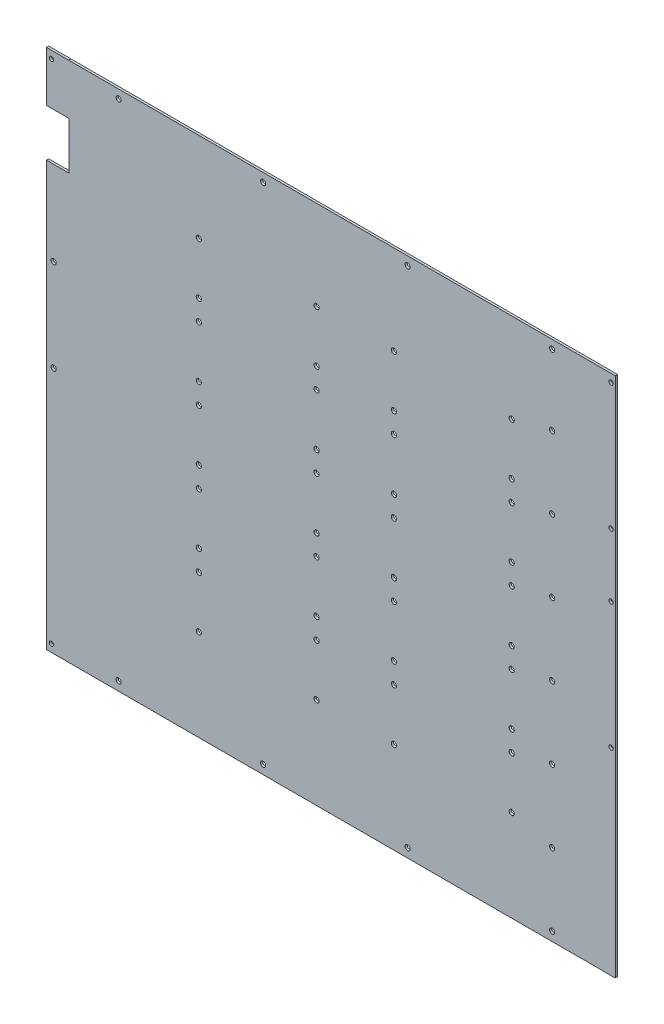
SolidWorks part; units mm, degrees
ref_plane "Front Plane" through (0, 0, 0) normal (0, 0, 1) x (1, 0, 0)
ref_plane "Top Plane" through (0, 0, 0) normal (0, 1, 0) x (1, 0, 0)
ref_plane "Right Plane" through (0, 0, 0) normal (1, 0, 0) x (0, 0, -1)
sketch "Model" plane through (0, 0, 0) normal (0, 0, 1) x (1, 0, 0)
  line L0 (0, 0) -> (400.05, 0)
  line L1 (400.05, 0) -> (400.05, 366.722)
  line L2 (400.05, 366.722) -> (15.6398, 366.7222)
  line L3 (15.6398, 366.7222) -> (0, 366.7222)
  line L4 (0, 366.7222) -> (0, 331.3716)
  line L5 (0, 331.3716) -> (15.748, 331.3716)
  line L6 (15.748, 331.3716) -> (15.748, 298.0477)
  line L7 (15.748, 298.0477) -> (0, 298.0477)
  line L8 (0, 298.0477) -> (0, 0)
  line L2009 (3.556, 361.188) -> (3.556, 361.696)
  line L2010 (3.302, 361.442) -> (3.81, 361.442)
  line L2011 (3.556, 361.188) -> (3.556, 361.696)
  line L2012 (3.302, 361.442) -> (3.81, 361.442)
  line L2013 (3.556, 361.188) -> (3.556, 361.696)
  line L2014 (3.302, 361.442) -> (3.81, 361.442)
  line L2015 (3.556, 361.188) -> (3.556, 361.696)
  line L2016 (3.302, 361.442) -> (3.81, 361.442)
  line L2017 (3.556, 361.188) -> (3.556, 361.696)
  line L2018 (3.302, 361.442) -> (3.81, 361.442)
  line L2019 (3.556, 361.188) -> (3.556, 361.696)
  line L2020 (3.302, 361.442) -> (3.81, 361.442)
  line L2021 (3.556, 361.188) -> (3.556, 361.696)
  line L2022 (3.302, 361.442) -> (3.81, 361.442)
  line L2023 (3.556, 361.188) -> (3.556, 361.696)
  line L2024 (3.302, 361.442) -> (3.81, 361.442)
  line L2025 (3.556, 5.08) -> (3.556, 5.588)
  line L2026 (3.302, 5.334) -> (3.81, 5.334)
  line L2027 (3.556, 5.08) -> (3.556, 5.588)
  line L2028 (3.302, 5.334) -> (3.81, 5.334)
  line L2029 (3.556, 5.08) -> (3.556, 5.588)
  line L2030 (3.302, 5.334) -> (3.81, 5.334)
  line L2031 (3.556, 5.08) -> (3.556, 5.588)
  line L2032 (3.302, 5.334) -> (3.81, 5.334)
  line L2033 (3.556, 5.08) -> (3.556, 5.588)
  line L2034 (3.302, 5.334) -> (3.81, 5.334)
  line L2035 (3.556, 5.08) -> (3.556, 5.588)
  line L2036 (3.302, 5.334) -> (3.81, 5.334)
  line L2037 (3.556, 5.08) -> (3.556, 5.588)
  line L2038 (3.302, 5.334) -> (3.81, 5.334)
  line L2039 (3.556, 5.08) -> (3.556, 5.588)
  line L2040 (3.302, 5.334) -> (3.81, 5.334)
  line L2041 (5.08, 238.506) -> (5.08, 239.014)
  line L2042 (4.826, 238.76) -> (5.334, 238.76)
  line L2043 (5.08, 238.506) -> (5.08, 239.014)
  line L2044 (4.826, 238.76) -> (5.334, 238.76)
  line L2045 (5.08, 238.506) -> (5.08, 239.014)
  line L2046 (4.826, 238.76) -> (5.334, 238.76)
  line L2047 (5.08, 238.506) -> (5.08, 239.014)
  line L2048 (4.826, 238.76) -> (5.334, 238.76)
  line L2049 (5.08, 238.506) -> (5.08, 239.014)
  line L2050 (4.826, 238.76) -> (5.334, 238.76)
  line L2051 (5.08, 238.506) -> (5.08, 239.014)
  line L2052 (4.826, 238.76) -> (5.334, 238.76)
  line L2053 (5.08, 238.506) -> (5.08, 239.014)
  line L2054 (4.826, 238.76) -> (5.334, 238.76)
  line L2055 (5.08, 238.506) -> (5.08, 239.014)
  line L2056 (4.826, 238.76) -> (5.334, 238.76)
  line L2057 (5.08, 173.736) -> (5.08, 174.244)
  line L2058 (4.826, 173.99) -> (5.334, 173.99)
  line L2059 (5.08, 173.736) -> (5.08, 174.244)
  line L2060 (4.826, 173.99) -> (5.334, 173.99)
  line L2061 (5.08, 173.736) -> (5.08, 174.244)
  line L2062 (4.826, 173.99) -> (5.334, 173.99)
  line L2063 (5.08, 173.736) -> (5.08, 174.244)
  line L2064 (4.826, 173.99) -> (5.334, 173.99)
  line L2065 (5.08, 173.736) -> (5.08, 174.244)
  line L2066 (4.826, 173.99) -> (5.334, 173.99)
  line L2067 (5.08, 173.736) -> (5.08, 174.244)
  line L2068 (4.826, 173.99) -> (5.334, 173.99)
  line L2069 (5.08, 173.736) -> (5.08, 174.244)
  line L2070 (4.826, 173.99) -> (5.334, 173.99)
  line L2071 (5.08, 173.736) -> (5.08, 174.244)
  line L2072 (4.826, 173.99) -> (5.334, 173.99)
  line L3769 (397.3068, 272.2372) -> (396.7988, 272.2372)
  line L3770 (397.0528, 271.9832) -> (397.0528, 272.4912)
  line L3771 (397.3068, 272.2372) -> (396.7988, 272.2372)
  line L3772 (397.0528, 271.9832) -> (397.0528, 272.4912)
  line L3773 (397.3068, 272.2372) -> (396.7988, 272.2372)
  line L3774 (397.0528, 271.9832) -> (397.0528, 272.4912)
  line L3775 (397.3068, 272.2372) -> (396.7988, 272.2372)
  line L3776 (397.0528, 271.9832) -> (397.0528, 272.4912)
  line L3777 (397.3068, 272.2372) -> (396.7988, 272.2372)
  line L3778 (397.0528, 271.9832) -> (397.0528, 272.4912)
  line L3779 (397.3068, 272.2372) -> (396.7988, 272.2372)
  line L3780 (397.0528, 271.9832) -> (397.0528, 272.4912)
  line L3781 (397.3068, 272.2372) -> (396.7988, 272.2372)
  line L3782 (397.0528, 271.9832) -> (397.0528, 272.4912)
  line L3783 (397.3068, 272.2372) -> (396.7988, 272.2372)
  line L3784 (397.0528, 271.9832) -> (397.0528, 272.4912)
  line L3785 (397.3068, 361.1372) -> (396.7988, 361.1372)
  line L3786 (397.0528, 360.8832) -> (397.0528, 361.3912)
  line L3787 (397.3068, 361.1372) -> (396.7988, 361.1372)
  line L3788 (397.0528, 360.8832) -> (397.0528, 361.3912)
  line L3789 (397.3068, 361.1372) -> (396.7988, 361.1372)
  line L3790 (397.0528, 360.8832) -> (397.0528, 361.3912)
  line L3791 (397.3068, 361.1372) -> (396.7988, 361.1372)
  line L3792 (397.0528, 360.8832) -> (397.0528, 361.3912)
  line L3793 (397.3068, 361.1372) -> (396.7988, 361.1372)
  line L3794 (397.0528, 360.8832) -> (397.0528, 361.3912)
  line L3795 (397.3068, 361.1372) -> (396.7988, 361.1372)
  line L3796 (397.0528, 360.8832) -> (397.0528, 361.3912)
  line L3797 (397.3068, 361.1372) -> (396.7988, 361.1372)
  line L3798 (397.0528, 360.8832) -> (397.0528, 361.3912)
  line L3799 (397.3068, 361.1372) -> (396.7988, 361.1372)
  line L3800 (397.0528, 360.8832) -> (397.0528, 361.3912)
  line L5337 (397.3068, 138.8872) -> (396.7988, 138.8872)
  line L5338 (397.0528, 138.6332) -> (397.0528, 139.1412)
  line L5339 (397.3068, 138.8872) -> (396.7988, 138.8872)
  line L5340 (397.0528, 138.6332) -> (397.0528, 139.1412)
  line L5341 (397.3068, 138.8872) -> (396.7988, 138.8872)
  line L5342 (397.0528, 138.6332) -> (397.0528, 139.1412)
  line L5343 (397.3068, 138.8872) -> (396.7988, 138.8872)
  line L5344 (397.0528, 138.6332) -> (397.0528, 139.1412)
  line L5345 (397.3068, 138.8872) -> (396.7988, 138.8872)
  line L5346 (397.0528, 138.6332) -> (397.0528, 139.1412)
  line L5347 (397.3068, 138.8872) -> (396.7988, 138.8872)
  line L5348 (397.0528, 138.6332) -> (397.0528, 139.1412)
  line L5349 (397.3068, 138.8872) -> (396.7988, 138.8872)
  line L5350 (397.0528, 138.6332) -> (397.0528, 139.1412)
  line L5351 (397.3068, 138.8872) -> (396.7988, 138.8872)
  line L5352 (397.0528, 138.6332) -> (397.0528, 139.1412)
  line L5353 (397.3068, 227.7872) -> (396.7988, 227.7872)
  line L5354 (397.0528, 227.5332) -> (397.0528, 228.0412)
  line L5355 (397.3068, 227.7872) -> (396.7988, 227.7872)
  line L5356 (397.0528, 227.5332) -> (397.0528, 228.0412)
  line L5357 (397.3068, 227.7872) -> (396.7988, 227.7872)
  line L5358 (397.0528, 227.5332) -> (397.0528, 228.0412)
  line L5359 (397.3068, 227.7872) -> (396.7988, 227.7872)
  line L5360 (397.0528, 227.5332) -> (397.0528, 228.0412)
  line L5361 (397.3068, 227.7872) -> (396.7988, 227.7872)
  line L5362 (397.0528, 227.5332) -> (397.0528, 228.0412)
  line L5363 (397.3068, 227.7872) -> (396.7988, 227.7872)
  line L5364 (397.0528, 227.5332) -> (397.0528, 228.0412)
  line L5365 (397.3068, 227.7872) -> (396.7988, 227.7872)
  line L5366 (397.0528, 227.5332) -> (397.0528, 228.0412)
  line L5367 (397.3068, 227.7872) -> (396.7988, 227.7872)
  line L5368 (397.0528, 227.5332) -> (397.0528, 228.0412)
  line L7017 (355.6, 360.426) -> (355.6, 360.934)
  line L7018 (355.346, 360.68) -> (355.854, 360.68)
  line L7019 (355.6, 360.426) -> (355.6, 360.934)
  line L7020 (355.346, 360.68) -> (355.854, 360.68)
  line L7021 (355.6, 360.426) -> (355.6, 360.934)
  line L7022 (355.346, 360.68) -> (355.854, 360.68)
  line L7023 (355.6, 360.426) -> (355.6, 360.934)
  line L7024 (355.346, 360.68) -> (355.854, 360.68)
  line L7025 (355.6, 360.426) -> (355.6, 360.934)
  line L7026 (355.346, 360.68) -> (355.854, 360.68)
  line L7027 (355.6, 360.426) -> (355.6, 360.934)
  line L7028 (355.346, 360.68) -> (355.854, 360.68)
  line L7029 (355.6, 360.426) -> (355.6, 360.934)
  line L7030 (355.346, 360.68) -> (355.854, 360.68)
  line L7031 (355.6, 360.426) -> (355.6, 360.934)
  line L7032 (355.346, 360.68) -> (355.854, 360.68)
  line L7033 (355.6, 310.896) -> (355.6, 311.404)
  line L7034 (355.346, 311.15) -> (355.854, 311.15)
  line L7035 (355.6, 310.896) -> (355.6, 311.404)
  line L7036 (355.346, 311.15) -> (355.854, 311.15)
  line L7037 (355.6, 310.896) -> (355.6, 311.404)
  line L7038 (355.346, 311.15) -> (355.854, 311.15)
  line L7039 (355.6, 310.896) -> (355.6, 311.404)
  line L7040 (355.346, 311.15) -> (355.854, 311.15)
  line L7041 (355.6, 310.896) -> (355.6, 311.404)
  line L7042 (355.346, 311.15) -> (355.854, 311.15)
  line L7043 (355.6, 310.896) -> (355.6, 311.404)
  line L7044 (355.346, 311.15) -> (355.854, 311.15)
  line L7045 (355.6, 310.896) -> (355.6, 311.404)
  line L7046 (355.346, 311.15) -> (355.854, 311.15)
  line L7047 (355.6, 310.896) -> (355.6, 311.404)
  line L7048 (355.346, 311.15) -> (355.854, 311.15)
  line L7049 (355.6, 260.096) -> (355.6, 260.604)
  line L7050 (355.346, 260.35) -> (355.854, 260.35)
  line L7051 (355.6, 260.096) -> (355.6, 260.604)
  line L7052 (355.346, 260.35) -> (355.854, 260.35)
  line L7053 (355.6, 260.096) -> (355.6, 260.604)
  line L7054 (355.346, 260.35) -> (355.854, 260.35)
  line L7055 (355.6, 260.096) -> (355.6, 260.604)
  line L7056 (355.346, 260.35) -> (355.854, 260.35)
  line L7057 (355.6, 260.096) -> (355.6, 260.604)
  line L7058 (355.346, 260.35) -> (355.854, 260.35)
  line L7059 (355.6, 260.096) -> (355.6, 260.604)
  line L7060 (355.346, 260.35) -> (355.854, 260.35)
  line L7061 (355.6, 260.096) -> (355.6, 260.604)
  line L7062 (355.346, 260.35) -> (355.854, 260.35)
  line L7063 (355.6, 260.096) -> (355.6, 260.604)
  line L7064 (355.346, 260.35) -> (355.854, 260.35)
  line L7065 (355.6, 209.296) -> (355.6, 209.804)
  line L7066 (355.346, 209.55) -> (355.854, 209.55)
  line L7067 (355.6, 209.296) -> (355.6, 209.804)
  line L7068 (355.346, 209.55) -> (355.854, 209.55)
  line L7069 (355.6, 209.296) -> (355.6, 209.804)
  line L7070 (355.346, 209.55) -> (355.854, 209.55)
  line L7071 (355.6, 209.296) -> (355.6, 209.804)
  line L7072 (355.346, 209.55) -> (355.854, 209.55)
  line L7073 (355.6, 209.296) -> (355.6, 209.804)
  line L7074 (355.346, 209.55) -> (355.854, 209.55)
  line L7075 (355.6, 209.296) -> (355.6, 209.804)
  line L7076 (355.346, 209.55) -> (355.854, 209.55)
  line L7077 (355.6, 209.296) -> (355.6, 209.804)
  line L7078 (355.346, 209.55) -> (355.854, 209.55)
  line L7079 (355.6, 209.296) -> (355.6, 209.804)
  line L7080 (355.346, 209.55) -> (355.854, 209.55)
  line L7081 (355.6, 158.496) -> (355.6, 159.004)
  line L7082 (355.346, 158.75) -> (355.854, 158.75)
  line L7083 (355.6, 158.496) -> (355.6, 159.004)
  line L7084 (355.346, 158.75) -> (355.854, 158.75)
  line L7085 (355.6, 158.496) -> (355.6, 159.004)
  line L7086 (355.346, 158.75) -> (355.854, 158.75)
  line L7087 (355.6, 158.496) -> (355.6, 159.004)
  line L7088 (355.346, 158.75) -> (355.854, 158.75)
  line L7089 (355.6, 158.496) -> (355.6, 159.004)
  line L7090 (355.346, 158.75) -> (355.854, 158.75)
  line L7091 (355.6, 158.496) -> (355.6, 159.004)
  line L7092 (355.346, 158.75) -> (355.854, 158.75)
  line L7093 (355.6, 158.496) -> (355.6, 159.004)
  line L7094 (355.346, 158.75) -> (355.854, 158.75)
  line L7095 (355.6, 158.496) -> (355.6, 159.004)
  line L7096 (355.346, 158.75) -> (355.854, 158.75)
  line L7097 (355.6, 107.696) -> (355.6, 108.204)
  line L7098 (355.346, 107.95) -> (355.854, 107.95)
  line L7099 (355.6, 107.696) -> (355.6, 108.204)
  line L7100 (355.346, 107.95) -> (355.854, 107.95)
  line L7101 (355.6, 107.696) -> (355.6, 108.204)
  line L7102 (355.346, 107.95) -> (355.854, 107.95)
  line L7103 (355.6, 107.696) -> (355.6, 108.204)
  line L7104 (355.346, 107.95) -> (355.854, 107.95)
  line L7105 (355.6, 107.696) -> (355.6, 108.204)
  line L7106 (355.346, 107.95) -> (355.854, 107.95)
  line L7107 (355.6, 107.696) -> (355.6, 108.204)
  line L7108 (355.346, 107.95) -> (355.854, 107.95)
  line L7109 (355.6, 107.696) -> (355.6, 108.204)
  line L7110 (355.346, 107.95) -> (355.854, 107.95)
  line L7111 (355.6, 107.696) -> (355.6, 108.204)
  line L7112 (355.346, 107.95) -> (355.854, 107.95)
  line L7113 (355.6, 56.896) -> (355.6, 57.404)
  line L7114 (355.346, 57.15) -> (355.854, 57.15)
  line L7115 (355.6, 56.896) -> (355.6, 57.404)
  line L7116 (355.346, 57.15) -> (355.854, 57.15)
  line L7117 (355.6, 56.896) -> (355.6, 57.404)
  line L7118 (355.346, 57.15) -> (355.854, 57.15)
  line L7119 (355.6, 56.896) -> (355.6, 57.404)
  line L7120 (355.346, 57.15) -> (355.854, 57.15)
  line L7121 (355.6, 56.896) -> (355.6, 57.404)
  line L7122 (355.346, 57.15) -> (355.854, 57.15)
  line L7123 (355.6, 56.896) -> (355.6, 57.404)
  line L7124 (355.346, 57.15) -> (355.854, 57.15)
  line L7125 (355.6, 56.896) -> (355.6, 57.404)
  line L7126 (355.346, 57.15) -> (355.854, 57.15)
  line L7127 (355.6, 56.896) -> (355.6, 57.404)
  line L7128 (355.346, 57.15) -> (355.854, 57.15)
  line L7129 (355.6, 6.096) -> (355.6, 6.604)
  line L7130 (355.346, 6.35) -> (355.854, 6.35)
  line L7131 (355.6, 6.096) -> (355.6, 6.604)
  line L7132 (355.346, 6.35) -> (355.854, 6.35)
  line L7133 (355.6, 6.096) -> (355.6, 6.604)
  line L7134 (355.346, 6.35) -> (355.854, 6.35)
  line L7135 (355.6, 6.096) -> (355.6, 6.604)
  line L7136 (355.346, 6.35) -> (355.854, 6.35)
  line L7137 (355.6, 6.096) -> (355.6, 6.604)
  line L7138 (355.346, 6.35) -> (355.854, 6.35)
  line L7139 (355.6, 6.096) -> (355.6, 6.604)
  line L7140 (355.346, 6.35) -> (355.854, 6.35)
  line L7141 (355.6, 6.096) -> (355.6, 6.604)
  line L7142 (355.346, 6.35) -> (355.854, 6.35)
  line L7143 (355.6, 6.096) -> (355.6, 6.604)
  line L7144 (355.346, 6.35) -> (355.854, 6.35)
  line L7145 (254, 360.426) -> (254, 360.934)
  line L7146 (253.746, 360.68) -> (254.254, 360.68)
  line L7147 (254, 360.426) -> (254, 360.934)
  line L7148 (253.746, 360.68) -> (254.254, 360.68)
  line L7149 (254, 360.426) -> (254, 360.934)
  line L7150 (253.746, 360.68) -> (254.254, 360.68)
  line L7151 (254, 360.426) -> (254, 360.934)
  line L7152 (253.746, 360.68) -> (254.254, 360.68)
  line L7153 (254, 360.426) -> (254, 360.934)
  line L7154 (253.746, 360.68) -> (254.254, 360.68)
  line L7155 (254, 360.426) -> (254, 360.934)
  line L7156 (253.746, 360.68) -> (254.254, 360.68)
  line L7157 (254, 360.426) -> (254, 360.934)
  line L7158 (253.746, 360.68) -> (254.254, 360.68)
  line L7159 (254, 360.426) -> (254, 360.934)
  line L7160 (253.746, 360.68) -> (254.254, 360.68)
  line L7161 (254, 6.096) -> (254, 6.604)
  line L7162 (253.746, 6.35) -> (254.254, 6.35)
  line L7163 (254, 6.096) -> (254, 6.604)
  line L7164 (253.746, 6.35) -> (254.254, 6.35)
  line L7165 (254, 6.096) -> (254, 6.604)
  line L7166 (253.746, 6.35) -> (254.254, 6.35)
  line L7167 (254, 6.096) -> (254, 6.604)
  line L7168 (253.746, 6.35) -> (254.254, 6.35)
  line L7169 (254, 6.096) -> (254, 6.604)
  line L7170 (253.746, 6.35) -> (254.254, 6.35)
  line L7171 (254, 6.096) -> (254, 6.604)
  line L7172 (253.746, 6.35) -> (254.254, 6.35)
  line L7173 (254, 6.096) -> (254, 6.604)
  line L7174 (253.746, 6.35) -> (254.254, 6.35)
  line L7175 (254, 6.096) -> (254, 6.604)
  line L7176 (253.746, 6.35) -> (254.254, 6.35)
  line L7273 (327.152, 267.843) -> (327.152, 267.335)
  line L7274 (327.406, 267.589) -> (326.898, 267.589)
  line L7275 (327.152, 267.843) -> (327.152, 267.335)
  line L7276 (327.406, 267.589) -> (326.898, 267.589)
  line L7277 (327.152, 267.843) -> (327.152, 267.335)
  line L7278 (327.406, 267.589) -> (326.898, 267.589)
  line L7279 (327.152, 267.843) -> (327.152, 267.335)
  line L7280 (327.406, 267.589) -> (326.898, 267.589)
  line L7281 (327.152, 267.843) -> (327.152, 267.335)
  line L7282 (327.406, 267.589) -> (326.898, 267.589)
  line L7283 (327.152, 267.843) -> (327.152, 267.335)
  line L7284 (327.406, 267.589) -> (326.898, 267.589)
  line L7285 (327.152, 267.843) -> (327.152, 267.335)
  line L7286 (327.406, 267.589) -> (326.898, 267.589)
  line L7287 (327.152, 267.843) -> (327.152, 267.335)
  line L7288 (327.406, 267.589) -> (326.898, 267.589)
  line L7289 (244.348, 267.843) -> (244.348, 267.335)
  line L7290 (244.602, 267.589) -> (244.094, 267.589)
  line L7291 (244.348, 267.843) -> (244.348, 267.335)
  line L7292 (244.602, 267.589) -> (244.094, 267.589)
  line L7293 (244.348, 267.843) -> (244.348, 267.335)
  line L7294 (244.602, 267.589) -> (244.094, 267.589)
  line L7295 (244.348, 267.843) -> (244.348, 267.335)
  line L7296 (244.602, 267.589) -> (244.094, 267.589)
  line L7297 (244.348, 267.843) -> (244.348, 267.335)
  line L7298 (244.602, 267.589) -> (244.094, 267.589)
  line L7299 (244.348, 267.843) -> (244.348, 267.335)
  line L7300 (244.602, 267.589) -> (244.094, 267.589)
  line L7301 (244.348, 267.843) -> (244.348, 267.335)
  line L7302 (244.602, 267.589) -> (244.094, 267.589)
  line L7303 (244.348, 267.843) -> (244.348, 267.335)
  line L7304 (244.602, 267.589) -> (244.094, 267.589)
  line L7305 (327.152, 304.165) -> (327.152, 303.657)
  line L7306 (327.406, 303.911) -> (326.898, 303.911)
  line L7307 (327.152, 304.165) -> (327.152, 303.657)
  line L7308 (327.406, 303.911) -> (326.898, 303.911)
  line L7309 (327.152, 304.165) -> (327.152, 303.657)
  line L7310 (327.406, 303.911) -> (326.898, 303.911)
  line L7311 (327.152, 304.165) -> (327.152, 303.657)
  line L7312 (327.406, 303.911) -> (326.898, 303.911)
  line L7313 (327.152, 304.165) -> (327.152, 303.657)
  line L7314 (327.406, 303.911) -> (326.898, 303.911)
  line L7315 (327.152, 304.165) -> (327.152, 303.657)
  line L7316 (327.406, 303.911) -> (326.898, 303.911)
  line L7317 (327.152, 304.165) -> (327.152, 303.657)
  line L7318 (327.406, 303.911) -> (326.898, 303.911)
  line L7319 (327.152, 304.165) -> (327.152, 303.657)
  line L7320 (327.406, 303.911) -> (326.898, 303.911)
  line L7321 (244.348, 304.165) -> (244.348, 303.657)
  line L7322 (244.602, 303.911) -> (244.094, 303.911)
  line L7323 (244.348, 304.165) -> (244.348, 303.657)
  line L7324 (244.602, 303.911) -> (244.094, 303.911)
  line L7325 (244.348, 304.165) -> (244.348, 303.657)
  line L7326 (244.602, 303.911) -> (244.094, 303.911)
  line L7327 (244.348, 304.165) -> (244.348, 303.657)
  line L7328 (244.602, 303.911) -> (244.094, 303.911)
  line L7329 (244.348, 304.165) -> (244.348, 303.657)
  line L7330 (244.602, 303.911) -> (244.094, 303.911)
  line L7331 (244.348, 304.165) -> (244.348, 303.657)
  line L7332 (244.602, 303.911) -> (244.094, 303.911)
  line L7333 (244.348, 304.165) -> (244.348, 303.657)
  line L7334 (244.602, 303.911) -> (244.094, 303.911)
  line L7335 (244.348, 304.165) -> (244.348, 303.657)
  line L7336 (244.602, 303.911) -> (244.094, 303.911)
  line L7433 (327.152, 217.043) -> (327.152, 216.535)
  line L7434 (327.406, 216.789) -> (326.898, 216.789)
  line L7435 (327.152, 217.043) -> (327.152, 216.535)
  line L7436 (327.406, 216.789) -> (326.898, 216.789)
  line L7437 (327.152, 217.043) -> (327.152, 216.535)
  line L7438 (327.406, 216.789) -> (326.898, 216.789)
  line L7439 (327.152, 217.043) -> (327.152, 216.535)
  line L7440 (327.406, 216.789) -> (326.898, 216.789)
  line L7441 (327.152, 217.043) -> (327.152, 216.535)
  line L7442 (327.406, 216.789) -> (326.898, 216.789)
  line L7443 (327.152, 217.043) -> (327.152, 216.535)
  line L7444 (327.406, 216.789) -> (326.898, 216.789)
  line L7445 (327.152, 217.043) -> (327.152, 216.535)
  line L7446 (327.406, 216.789) -> (326.898, 216.789)
  line L7447 (327.152, 217.043) -> (327.152, 216.535)
  line L7448 (327.406, 216.789) -> (326.898, 216.789)
  line L7449 (244.348, 217.043) -> (244.348, 216.535)
  line L7450 (244.602, 216.789) -> (244.094, 216.789)
  line L7451 (244.348, 217.043) -> (244.348, 216.535)
  line L7452 (244.602, 216.789) -> (244.094, 216.789)
  line L7453 (244.348, 217.043) -> (244.348, 216.535)
  line L7454 (244.602, 216.789) -> (244.094, 216.789)
  line L7455 (244.348, 217.043) -> (244.348, 216.535)
  line L7456 (244.602, 216.789) -> (244.094, 216.789)
  line L7457 (244.348, 217.043) -> (244.348, 216.535)
  line L7458 (244.602, 216.789) -> (244.094, 216.789)
  line L7459 (244.348, 217.043) -> (244.348, 216.535)
  line L7460 (244.602, 216.789) -> (244.094, 216.789)
  line L7461 (244.348, 217.043) -> (244.348, 216.535)
  line L7462 (244.602, 216.789) -> (244.094, 216.789)
  line L7463 (244.348, 217.043) -> (244.348, 216.535)
  line L7464 (244.602, 216.789) -> (244.094, 216.789)
  line L7465 (327.152, 253.365) -> (327.152, 252.857)
  line L7466 (327.406, 253.111) -> (326.898, 253.111)
  line L7467 (327.152, 253.365) -> (327.152, 252.857)
  line L7468 (327.406, 253.111) -> (326.898, 253.111)
  line L7469 (327.152, 253.365) -> (327.152, 252.857)
  line L7470 (327.406, 253.111) -> (326.898, 253.111)
  line L7471 (327.152, 253.365) -> (327.152, 252.857)
  line L7472 (327.406, 253.111) -> (326.898, 253.111)
  line L7473 (327.152, 253.365) -> (327.152, 252.857)
  line L7474 (327.406, 253.111) -> (326.898, 253.111)
  line L7475 (327.152, 253.365) -> (327.152, 252.857)
  line L7476 (327.406, 253.111) -> (326.898, 253.111)
  line L7477 (327.152, 253.365) -> (327.152, 252.857)
  line L7478 (327.406, 253.111) -> (326.898, 253.111)
  line L7479 (327.152, 253.365) -> (327.152, 252.857)
  line L7480 (327.406, 253.111) -> (326.898, 253.111)
  line L7481 (244.348, 253.365) -> (244.348, 252.857)
  line L7482 (244.602, 253.111) -> (244.094, 253.111)
  line L7483 (244.348, 253.365) -> (244.348, 252.857)
  line L7484 (244.602, 253.111) -> (244.094, 253.111)
  line L7485 (244.348, 253.365) -> (244.348, 252.857)
  line L7486 (244.602, 253.111) -> (244.094, 253.111)
  line L7487 (244.348, 253.365) -> (244.348, 252.857)
  line L7488 (244.602, 253.111) -> (244.094, 253.111)
  line L7489 (244.348, 253.365) -> (244.348, 252.857)
  line L7490 (244.602, 253.111) -> (244.094, 253.111)
  line L7491 (244.348, 253.365) -> (244.348, 252.857)
  line L7492 (244.602, 253.111) -> (244.094, 253.111)
  line L7493 (244.348, 253.365) -> (244.348, 252.857)
  line L7494 (244.602, 253.111) -> (244.094, 253.111)
  line L7495 (244.348, 253.365) -> (244.348, 252.857)
  line L7496 (244.602, 253.111) -> (244.094, 253.111)
  line L7593 (327.152, 166.243) -> (327.152, 165.735)
  line L7594 (327.406, 165.989) -> (326.898, 165.989)
  line L7595 (327.152, 166.243) -> (327.152, 165.735)
  line L7596 (327.406, 165.989) -> (326.898, 165.989)
  line L7597 (327.152, 166.243) -> (327.152, 165.735)
  line L7598 (327.406, 165.989) -> (326.898, 165.989)
  line L7599 (327.152, 166.243) -> (327.152, 165.735)
  line L7600 (327.406, 165.989) -> (326.898, 165.989)
  line L7601 (327.152, 166.243) -> (327.152, 165.735)
  line L7602 (327.406, 165.989) -> (326.898, 165.989)
  line L7603 (327.152, 166.243) -> (327.152, 165.735)
  line L7604 (327.406, 165.989) -> (326.898, 165.989)
  line L7605 (327.152, 166.243) -> (327.152, 165.735)
  line L7606 (327.406, 165.989) -> (326.898, 165.989)
  line L7607 (327.152, 166.243) -> (327.152, 165.735)
  line L7608 (327.406, 165.989) -> (326.898, 165.989)
  line L7609 (244.348, 166.243) -> (244.348, 165.735)
  line L7610 (244.602, 165.989) -> (244.094, 165.989)
  line L7611 (244.348, 166.243) -> (244.348, 165.735)
  line L7612 (244.602, 165.989) -> (244.094, 165.989)
  line L7613 (244.348, 166.243) -> (244.348, 165.735)
  line L7614 (244.602, 165.989) -> (244.094, 165.989)
  line L7615 (244.348, 166.243) -> (244.348, 165.735)
  line L7616 (244.602, 165.989) -> (244.094, 165.989)
  line L7617 (244.348, 166.243) -> (244.348, 165.735)
  line L7618 (244.602, 165.989) -> (244.094, 165.989)
  line L7619 (244.348, 166.243) -> (244.348, 165.735)
  line L7620 (244.602, 165.989) -> (244.094, 165.989)
  line L7621 (244.348, 166.243) -> (244.348, 165.735)
  line L7622 (244.602, 165.989) -> (244.094, 165.989)
  line L7623 (244.348, 166.243) -> (244.348, 165.735)
  line L7624 (244.602, 165.989) -> (244.094, 165.989)
  line L7625 (327.152, 202.565) -> (327.152, 202.057)
  line L7626 (327.406, 202.311) -> (326.898, 202.311)
  line L7627 (327.152, 202.565) -> (327.152, 202.057)
  line L7628 (327.406, 202.311) -> (326.898, 202.311)
  line L7629 (327.152, 202.565) -> (327.152, 202.057)
  line L7630 (327.406, 202.311) -> (326.898, 202.311)
  line L7631 (327.152, 202.565) -> (327.152, 202.057)
  line L7632 (327.406, 202.311) -> (326.898, 202.311)
  line L7633 (327.152, 202.565) -> (327.152, 202.057)
  line L7634 (327.406, 202.311) -> (326.898, 202.311)
  line L7635 (327.152, 202.565) -> (327.152, 202.057)
  line L7636 (327.406, 202.311) -> (326.898, 202.311)
  line L7637 (327.152, 202.565) -> (327.152, 202.057)
  line L7638 (327.406, 202.311) -> (326.898, 202.311)
  line L7639 (327.152, 202.565) -> (327.152, 202.057)
  line L7640 (327.406, 202.311) -> (326.898, 202.311)
  line L7641 (244.348, 202.565) -> (244.348, 202.057)
  line L7642 (244.602, 202.311) -> (244.094, 202.311)
  line L7643 (244.348, 202.565) -> (244.348, 202.057)
  line L7644 (244.602, 202.311) -> (244.094, 202.311)
  line L7645 (244.348, 202.565) -> (244.348, 202.057)
  line L7646 (244.602, 202.311) -> (244.094, 202.311)
  line L7647 (244.348, 202.565) -> (244.348, 202.057)
  line L7648 (244.602, 202.311) -> (244.094, 202.311)
  line L7649 (244.348, 202.565) -> (244.348, 202.057)
  line L7650 (244.602, 202.311) -> (244.094, 202.311)
  line L7651 (244.348, 202.565) -> (244.348, 202.057)
  line L7652 (244.602, 202.311) -> (244.094, 202.311)
  line L7653 (244.348, 202.565) -> (244.348, 202.057)
  line L7654 (244.602, 202.311) -> (244.094, 202.311)
  line L7655 (244.348, 202.565) -> (244.348, 202.057)
  line L7656 (244.602, 202.311) -> (244.094, 202.311)
  line L7753 (327.152, 115.443) -> (327.152, 114.935)
  line L7754 (327.406, 115.189) -> (326.898, 115.189)
  line L7755 (327.152, 115.443) -> (327.152, 114.935)
  line L7756 (327.406, 115.189) -> (326.898, 115.189)
  line L7757 (327.152, 115.443) -> (327.152, 114.935)
  line L7758 (327.406, 115.189) -> (326.898, 115.189)
  line L7759 (327.152, 115.443) -> (327.152, 114.935)
  line L7760 (327.406, 115.189) -> (326.898, 115.189)
  line L7761 (327.152, 115.443) -> (327.152, 114.935)
  line L7762 (327.406, 115.189) -> (326.898, 115.189)
  line L7763 (327.152, 115.443) -> (327.152, 114.935)
  line L7764 (327.406, 115.189) -> (326.898, 115.189)
  line L7765 (327.152, 115.443) -> (327.152, 114.935)
  line L7766 (327.406, 115.189) -> (326.898, 115.189)
  line L7767 (327.152, 115.443) -> (327.152, 114.935)
  line L7768 (327.406, 115.189) -> (326.898, 115.189)
  line L7769 (244.348, 115.443) -> (244.348, 114.935)
  line L7770 (244.602, 115.189) -> (244.094, 115.189)
  line L7771 (244.348, 115.443) -> (244.348, 114.935)
  line L7772 (244.602, 115.189) -> (244.094, 115.189)
  line L7773 (244.348, 115.443) -> (244.348, 114.935)
  line L7774 (244.602, 115.189) -> (244.094, 115.189)
  line L7775 (244.348, 115.443) -> (244.348, 114.935)
  line L7776 (244.602, 115.189) -> (244.094, 115.189)
  line L7777 (244.348, 115.443) -> (244.348, 114.935)
  line L7778 (244.602, 115.189) -> (244.094, 115.189)
  line L7779 (244.348, 115.443) -> (244.348, 114.935)
  line L7780 (244.602, 115.189) -> (244.094, 115.189)
  line L7781 (244.348, 115.443) -> (244.348, 114.935)
  line L7782 (244.602, 115.189) -> (244.094, 115.189)
  line L7783 (244.348, 115.443) -> (244.348, 114.935)
  line L7784 (244.602, 115.189) -> (244.094, 115.189)
  line L7785 (327.152, 151.765) -> (327.152, 151.257)
  line L7786 (327.406, 151.511) -> (326.898, 151.511)
  line L7787 (327.152, 151.765) -> (327.152, 151.257)
  line L7788 (327.406, 151.511) -> (326.898, 151.511)
  line L7789 (327.152, 151.765) -> (327.152, 151.257)
  line L7790 (327.406, 151.511) -> (326.898, 151.511)
  line L7791 (327.152, 151.765) -> (327.152, 151.257)
  line L7792 (327.406, 151.511) -> (326.898, 151.511)
  line L7793 (327.152, 151.765) -> (327.152, 151.257)
  line L7794 (327.406, 151.511) -> (326.898, 151.511)
  line L7795 (327.152, 151.765) -> (327.152, 151.257)
  line L7796 (327.406, 151.511) -> (326.898, 151.511)
  line L7797 (327.152, 151.765) -> (327.152, 151.257)
  line L7798 (327.406, 151.511) -> (326.898, 151.511)
  line L7799 (327.152, 151.765) -> (327.152, 151.257)
  line L7800 (327.406, 151.511) -> (326.898, 151.511)
  line L7801 (244.348, 151.765) -> (244.348, 151.257)
  line L7802 (244.602, 151.511) -> (244.094, 151.511)
  line L7803 (244.348, 151.765) -> (244.348, 151.257)
  line L7804 (244.602, 151.511) -> (244.094, 151.511)
  line L7805 (244.348, 151.765) -> (244.348, 151.257)
  line L7806 (244.602, 151.511) -> (244.094, 151.511)
  line L7807 (244.348, 151.765) -> (244.348, 151.257)
  line L7808 (244.602, 151.511) -> (244.094, 151.511)
  line L7809 (244.348, 151.765) -> (244.348, 151.257)
  line L7810 (244.602, 151.511) -> (244.094, 151.511)
  line L7811 (244.348, 151.765) -> (244.348, 151.257)
  line L7812 (244.602, 151.511) -> (244.094, 151.511)
  line L7813 (244.348, 151.765) -> (244.348, 151.257)
  line L7814 (244.602, 151.511) -> (244.094, 151.511)
  line L7815 (244.348, 151.765) -> (244.348, 151.257)
  line L7816 (244.602, 151.511) -> (244.094, 151.511)
  line L7913 (327.152, 64.643) -> (327.152, 64.135)
  line L7914 (327.406, 64.389) -> (326.898, 64.389)
  line L7915 (327.152, 64.643) -> (327.152, 64.135)
  line L7916 (327.406, 64.389) -> (326.898, 64.389)
  line L7917 (327.152, 64.643) -> (327.152, 64.135)
  line L7918 (327.406, 64.389) -> (326.898, 64.389)
  line L7919 (327.152, 64.643) -> (327.152, 64.135)
  line L7920 (327.406, 64.389) -> (326.898, 64.389)
  line L7921 (327.152, 64.643) -> (327.152, 64.135)
  line L7922 (327.406, 64.389) -> (326.898, 64.389)
  line L7923 (327.152, 64.643) -> (327.152, 64.135)
  line L7924 (327.406, 64.389) -> (326.898, 64.389)
  line L7925 (327.152, 64.643) -> (327.152, 64.135)
  line L7926 (327.406, 64.389) -> (326.898, 64.389)
  line L7927 (327.152, 64.643) -> (327.152, 64.135)
  line L7928 (327.406, 64.389) -> (326.898, 64.389)
  line L7929 (244.348, 64.643) -> (244.348, 64.135)
  line L7930 (244.602, 64.389) -> (244.094, 64.389)
  line L7931 (244.348, 64.643) -> (244.348, 64.135)
  line L7932 (244.602, 64.389) -> (244.094, 64.389)
  line L7933 (244.348, 64.643) -> (244.348, 64.135)
  line L7934 (244.602, 64.389) -> (244.094, 64.389)
  line L7935 (244.348, 64.643) -> (244.348, 64.135)
  line L7936 (244.602, 64.389) -> (244.094, 64.389)
  line L7937 (244.348, 64.643) -> (244.348, 64.135)
  line L7938 (244.602, 64.389) -> (244.094, 64.389)
  line L7939 (244.348, 64.643) -> (244.348, 64.135)
  line L7940 (244.602, 64.389) -> (244.094, 64.389)
  line L7941 (244.348, 64.643) -> (244.348, 64.135)
  line L7942 (244.602, 64.389) -> (244.094, 64.389)
  line L7943 (244.348, 64.643) -> (244.348, 64.135)
  line L7944 (244.602, 64.389) -> (244.094, 64.389)
  line L7945 (327.152, 100.965) -> (327.152, 100.457)
  line L7946 (327.406, 100.711) -> (326.898, 100.711)
  line L7947 (327.152, 100.965) -> (327.152, 100.457)
  line L7948 (327.406, 100.711) -> (326.898, 100.711)
  line L7949 (327.152, 100.965) -> (327.152, 100.457)
  line L7950 (327.406, 100.711) -> (326.898, 100.711)
  line L7951 (327.152, 100.965) -> (327.152, 100.457)
  line L7952 (327.406, 100.711) -> (326.898, 100.711)
  line L7953 (327.152, 100.965) -> (327.152, 100.457)
  line L7954 (327.406, 100.711) -> (326.898, 100.711)
  line L7955 (327.152, 100.965) -> (327.152, 100.457)
  line L7956 (327.406, 100.711) -> (326.898, 100.711)
  line L7957 (327.152, 100.965) -> (327.152, 100.457)
  line L7958 (327.406, 100.711) -> (326.898, 100.711)
  line L7959 (327.152, 100.965) -> (327.152, 100.457)
  line L7960 (327.406, 100.711) -> (326.898, 100.711)
  line L7961 (244.348, 100.965) -> (244.348, 100.457)
  line L7962 (244.602, 100.711) -> (244.094, 100.711)
  line L7963 (244.348, 100.965) -> (244.348, 100.457)
  line L7964 (244.602, 100.711) -> (244.094, 100.711)
  line L7965 (244.348, 100.965) -> (244.348, 100.457)
  line L7966 (244.602, 100.711) -> (244.094, 100.711)
  line L7967 (244.348, 100.965) -> (244.348, 100.457)
  line L7968 (244.602, 100.711) -> (244.094, 100.711)
  line L7969 (244.348, 100.965) -> (244.348, 100.457)
  line L7970 (244.602, 100.711) -> (244.094, 100.711)
  line L7971 (244.348, 100.965) -> (244.348, 100.457)
  line L7972 (244.602, 100.711) -> (244.094, 100.711)
  line L7973 (244.348, 100.965) -> (244.348, 100.457)
  line L7974 (244.602, 100.711) -> (244.094, 100.711)
  line L7975 (244.348, 100.965) -> (244.348, 100.457)
  line L7976 (244.602, 100.711) -> (244.094, 100.711)
  line L7977 (152.4, 360.426) -> (152.4, 360.934)
  line L7978 (152.146, 360.68) -> (152.654, 360.68)
  line L7979 (152.4, 360.426) -> (152.4, 360.934)
  line L7980 (152.146, 360.68) -> (152.654, 360.68)
  line L7981 (152.4, 360.426) -> (152.4, 360.934)
  line L7982 (152.146, 360.68) -> (152.654, 360.68)
  line L7983 (152.4, 360.426) -> (152.4, 360.934)
  line L7984 (152.146, 360.68) -> (152.654, 360.68)
  line L7985 (152.4, 360.426) -> (152.4, 360.934)
  line L7986 (152.146, 360.68) -> (152.654, 360.68)
  line L7987 (152.4, 360.426) -> (152.4, 360.934)
  line L7988 (152.146, 360.68) -> (152.654, 360.68)
  line L7989 (152.4, 360.426) -> (152.4, 360.934)
  line L7990 (152.146, 360.68) -> (152.654, 360.68)
  line L7991 (152.4, 360.426) -> (152.4, 360.934)
  line L7992 (152.146, 360.68) -> (152.654, 360.68)
  line L7993 (152.4, 6.096) -> (152.4, 6.604)
  line L7994 (152.146, 6.35) -> (152.654, 6.35)
  line L7995 (152.4, 6.096) -> (152.4, 6.604)
  line L7996 (152.146, 6.35) -> (152.654, 6.35)
  line L7997 (152.4, 6.096) -> (152.4, 6.604)
  line L7998 (152.146, 6.35) -> (152.654, 6.35)
  line L7999 (152.4, 6.096) -> (152.4, 6.604)
  line L8000 (152.146, 6.35) -> (152.654, 6.35)
  line L8001 (152.4, 6.096) -> (152.4, 6.604)
  line L8002 (152.146, 6.35) -> (152.654, 6.35)
  line L8003 (152.4, 6.096) -> (152.4, 6.604)
  line L8004 (152.146, 6.35) -> (152.654, 6.35)
  line L8005 (152.4, 6.096) -> (152.4, 6.604)
  line L8006 (152.146, 6.35) -> (152.654, 6.35)
  line L8007 (152.4, 6.096) -> (152.4, 6.604)
  line L8008 (152.146, 6.35) -> (152.654, 6.35)
  line L8105 (107.188, 303.657) -> (107.188, 304.165)
  line L8106 (106.934, 303.911) -> (107.442, 303.911)
  line L8107 (107.188, 303.657) -> (107.188, 304.165)
  line L8108 (106.934, 303.911) -> (107.442, 303.911)
  line L8109 (107.188, 303.657) -> (107.188, 304.165)
  line L8110 (106.934, 303.911) -> (107.442, 303.911)
  line L8111 (107.188, 303.657) -> (107.188, 304.165)
  line L8112 (106.934, 303.911) -> (107.442, 303.911)
  line L8113 (107.188, 303.657) -> (107.188, 304.165)
  line L8114 (106.934, 303.911) -> (107.442, 303.911)
  line L8115 (107.188, 303.657) -> (107.188, 304.165)
  line L8116 (106.934, 303.911) -> (107.442, 303.911)
  line L8117 (107.188, 303.657) -> (107.188, 304.165)
  line L8118 (106.934, 303.911) -> (107.442, 303.911)
  line L8119 (107.188, 303.657) -> (107.188, 304.165)
  line L8120 (106.934, 303.911) -> (107.442, 303.911)
  line L8121 (189.992, 303.657) -> (189.992, 304.165)
  line L8122 (189.738, 303.911) -> (190.246, 303.911)
  line L8123 (189.992, 303.657) -> (189.992, 304.165)
  line L8124 (189.738, 303.911) -> (190.246, 303.911)
  line L8125 (189.992, 303.657) -> (189.992, 304.165)
  line L8126 (189.738, 303.911) -> (190.246, 303.911)
  line L8127 (189.992, 303.657) -> (189.992, 304.165)
  line L8128 (189.738, 303.911) -> (190.246, 303.911)
  line L8129 (189.992, 303.657) -> (189.992, 304.165)
  line L8130 (189.738, 303.911) -> (190.246, 303.911)
  line L8131 (189.992, 303.657) -> (189.992, 304.165)
  line L8132 (189.738, 303.911) -> (190.246, 303.911)
  line L8133 (189.992, 303.657) -> (189.992, 304.165)
  line L8134 (189.738, 303.911) -> (190.246, 303.911)
  line L8135 (189.992, 303.657) -> (189.992, 304.165)
  line L8136 (189.738, 303.911) -> (190.246, 303.911)
  line L8137 (107.188, 267.335) -> (107.188, 267.843)
  line L8138 (106.934, 267.589) -> (107.442, 267.589)
  line L8139 (107.188, 267.335) -> (107.188, 267.843)
  line L8140 (106.934, 267.589) -> (107.442, 267.589)
  line L8141 (107.188, 267.335) -> (107.188, 267.843)
  line L8142 (106.934, 267.589) -> (107.442, 267.589)
  line L8143 (107.188, 267.335) -> (107.188, 267.843)
  line L8144 (106.934, 267.589) -> (107.442, 267.589)
  line L8145 (107.188, 267.335) -> (107.188, 267.843)
  line L8146 (106.934, 267.589) -> (107.442, 267.589)
  line L8147 (107.188, 267.335) -> (107.188, 267.843)
  line L8148 (106.934, 267.589) -> (107.442, 267.589)
  line L8149 (107.188, 267.335) -> (107.188, 267.843)
  line L8150 (106.934, 267.589) -> (107.442, 267.589)
  line L8151 (107.188, 267.335) -> (107.188, 267.843)
  line L8152 (106.934, 267.589) -> (107.442, 267.589)
  line L8153 (189.992, 267.335) -> (189.992, 267.843)
  line L8154 (189.738, 267.589) -> (190.246, 267.589)
  line L8155 (189.992, 267.335) -> (189.992, 267.843)
  line L8156 (189.738, 267.589) -> (190.246, 267.589)
  line L8157 (189.992, 267.335) -> (189.992, 267.843)
  line L8158 (189.738, 267.589) -> (190.246, 267.589)
  line L8159 (189.992, 267.335) -> (189.992, 267.843)
  line L8160 (189.738, 267.589) -> (190.246, 267.589)
  line L8161 (189.992, 267.335) -> (189.992, 267.843)
  line L8162 (189.738, 267.589) -> (190.246, 267.589)
  line L8163 (189.992, 267.335) -> (189.992, 267.843)
  line L8164 (189.738, 267.589) -> (190.246, 267.589)
  line L8165 (189.992, 267.335) -> (189.992, 267.843)
  line L8166 (189.738, 267.589) -> (190.246, 267.589)
  line L8167 (189.992, 267.335) -> (189.992, 267.843)
  line L8168 (189.738, 267.589) -> (190.246, 267.589)
  line L8265 (107.188, 252.857) -> (107.188, 253.365)
  line L8266 (106.934, 253.111) -> (107.442, 253.111)
  line L8267 (107.188, 252.857) -> (107.188, 253.365)
  line L8268 (106.934, 253.111) -> (107.442, 253.111)
  line L8269 (107.188, 252.857) -> (107.188, 253.365)
  line L8270 (106.934, 253.111) -> (107.442, 253.111)
  line L8271 (107.188, 252.857) -> (107.188, 253.365)
  line L8272 (106.934, 253.111) -> (107.442, 253.111)
  line L8273 (107.188, 252.857) -> (107.188, 253.365)
  line L8274 (106.934, 253.111) -> (107.442, 253.111)
  line L8275 (107.188, 252.857) -> (107.188, 253.365)
  line L8276 (106.934, 253.111) -> (107.442, 253.111)
  line L8277 (107.188, 252.857) -> (107.188, 253.365)
  line L8278 (106.934, 253.111) -> (107.442, 253.111)
  line L8279 (107.188, 252.857) -> (107.188, 253.365)
  line L8280 (106.934, 253.111) -> (107.442, 253.111)
  line L8281 (189.992, 252.857) -> (189.992, 253.365)
  line L8282 (189.738, 253.111) -> (190.246, 253.111)
  line L8283 (189.992, 252.857) -> (189.992, 253.365)
  line L8284 (189.738, 253.111) -> (190.246, 253.111)
  line L8285 (189.992, 252.857) -> (189.992, 253.365)
  line L8286 (189.738, 253.111) -> (190.246, 253.111)
  line L8287 (189.992, 252.857) -> (189.992, 253.365)
  line L8288 (189.738, 253.111) -> (190.246, 253.111)
  line L8289 (189.992, 252.857) -> (189.992, 253.365)
  line L8290 (189.738, 253.111) -> (190.246, 253.111)
  line L8291 (189.992, 252.857) -> (189.992, 253.365)
  line L8292 (189.738, 253.111) -> (190.246, 253.111)
  line L8293 (189.992, 252.857) -> (189.992, 253.365)
  line L8294 (189.738, 253.111) -> (190.246, 253.111)
  line L8295 (189.992, 252.857) -> (189.992, 253.365)
  line L8296 (189.738, 253.111) -> (190.246, 253.111)
  line L8297 (107.188, 216.535) -> (107.188, 217.043)
  line L8298 (106.934, 216.789) -> (107.442, 216.789)
  line L8299 (107.188, 216.535) -> (107.188, 217.043)
  line L8300 (106.934, 216.789) -> (107.442, 216.789)
  line L8301 (107.188, 216.535) -> (107.188, 217.043)
  line L8302 (106.934, 216.789) -> (107.442, 216.789)
  line L8303 (107.188, 216.535) -> (107.188, 217.043)
  line L8304 (106.934, 216.789) -> (107.442, 216.789)
  line L8305 (107.188, 216.535) -> (107.188, 217.043)
  line L8306 (106.934, 216.789) -> (107.442, 216.789)
  line L8307 (107.188, 216.535) -> (107.188, 217.043)
  line L8308 (106.934, 216.789) -> (107.442, 216.789)
  line L8309 (107.188, 216.535) -> (107.188, 217.043)
  line L8310 (106.934, 216.789) -> (107.442, 216.789)
  line L8311 (107.188, 216.535) -> (107.188, 217.043)
  line L8312 (106.934, 216.789) -> (107.442, 216.789)
  line L8313 (189.992, 216.535) -> (189.992, 217.043)
  line L8314 (189.738, 216.789) -> (190.246, 216.789)
  line L8315 (189.992, 216.535) -> (189.992, 217.043)
  line L8316 (189.738, 216.789) -> (190.246, 216.789)
  line L8317 (189.992, 216.535) -> (189.992, 217.043)
  line L8318 (189.738, 216.789) -> (190.246, 216.789)
  line L8319 (189.992, 216.535) -> (189.992, 217.043)
  line L8320 (189.738, 216.789) -> (190.246, 216.789)
  line L8321 (189.992, 216.535) -> (189.992, 217.043)
  line L8322 (189.738, 216.789) -> (190.246, 216.789)
  line L8323 (189.992, 216.535) -> (189.992, 217.043)
  line L8324 (189.738, 216.789) -> (190.246, 216.789)
  line L8325 (189.992, 216.535) -> (189.992, 217.043)
  line L8326 (189.738, 216.789) -> (190.246, 216.789)
  line L8327 (189.992, 216.535) -> (189.992, 217.043)
  line L8328 (189.738, 216.789) -> (190.246, 216.789)
  line L8425 (107.188, 202.057) -> (107.188, 202.565)
  line L8426 (106.934, 202.311) -> (107.442, 202.311)
  line L8427 (107.188, 202.057) -> (107.188, 202.565)
  line L8428 (106.934, 202.311) -> (107.442, 202.311)
  line L8429 (107.188, 202.057) -> (107.188, 202.565)
  line L8430 (106.934, 202.311) -> (107.442, 202.311)
  line L8431 (107.188, 202.057) -> (107.188, 202.565)
  line L8432 (106.934, 202.311) -> (107.442, 202.311)
  line L8433 (107.188, 202.057) -> (107.188, 202.565)
  line L8434 (106.934, 202.311) -> (107.442, 202.311)
  line L8435 (107.188, 202.057) -> (107.188, 202.565)
  line L8436 (106.934, 202.311) -> (107.442, 202.311)
  line L8437 (107.188, 202.057) -> (107.188, 202.565)
  line L8438 (106.934, 202.311) -> (107.442, 202.311)
  line L8439 (107.188, 202.057) -> (107.188, 202.565)
  line L8440 (106.934, 202.311) -> (107.442, 202.311)
  line L8441 (189.992, 202.057) -> (189.992, 202.565)
  line L8442 (189.738, 202.311) -> (190.246, 202.311)
  line L8443 (189.992, 202.057) -> (189.992, 202.565)
  line L8444 (189.738, 202.311) -> (190.246, 202.311)
  line L8445 (189.992, 202.057) -> (189.992, 202.565)
  line L8446 (189.738, 202.311) -> (190.246, 202.311)
  line L8447 (189.992, 202.057) -> (189.992, 202.565)
  line L8448 (189.738, 202.311) -> (190.246, 202.311)
  line L8449 (189.992, 202.057) -> (189.992, 202.565)
  line L8450 (189.738, 202.311) -> (190.246, 202.311)
  line L8451 (189.992, 202.057) -> (189.992, 202.565)
  line L8452 (189.738, 202.311) -> (190.246, 202.311)
  line L8453 (189.992, 202.057) -> (189.992, 202.565)
  line L8454 (189.738, 202.311) -> (190.246, 202.311)
  line L8455 (189.992, 202.057) -> (189.992, 202.565)
  line L8456 (189.738, 202.311) -> (190.246, 202.311)
  line L8457 (107.188, 165.735) -> (107.188, 166.243)
  line L8458 (106.934, 165.989) -> (107.442, 165.989)
  line L8459 (107.188, 165.735) -> (107.188, 166.243)
  line L8460 (106.934, 165.989) -> (107.442, 165.989)
  line L8461 (107.188, 165.735) -> (107.188, 166.243)
  line L8462 (106.934, 165.989) -> (107.442, 165.989)
  line L8463 (107.188, 165.735) -> (107.188, 166.243)
  line L8464 (106.934, 165.989) -> (107.442, 165.989)
  line L8465 (107.188, 165.735) -> (107.188, 166.243)
  line L8466 (106.934, 165.989) -> (107.442, 165.989)
  line L8467 (107.188, 165.735) -> (107.188, 166.243)
  line L8468 (106.934, 165.989) -> (107.442, 165.989)
  line L8469 (107.188, 165.735) -> (107.188, 166.243)
  line L8470 (106.934, 165.989) -> (107.442, 165.989)
  line L8471 (107.188, 165.735) -> (107.188, 166.243)
  line L8472 (106.934, 165.989) -> (107.442, 165.989)
  line L8473 (189.992, 165.735) -> (189.992, 166.243)
  line L8474 (189.738, 165.989) -> (190.246, 165.989)
  line L8475 (189.992, 165.735) -> (189.992, 166.243)
  line L8476 (189.738, 165.989) -> (190.246, 165.989)
  line L8477 (189.992, 165.735) -> (189.992, 166.243)
  line L8478 (189.738, 165.989) -> (190.246, 165.989)
  line L8479 (189.992, 165.735) -> (189.992, 166.243)
  line L8480 (189.738, 165.989) -> (190.246, 165.989)
  line L8481 (189.992, 165.735) -> (189.992, 166.243)
  line L8482 (189.738, 165.989) -> (190.246, 165.989)
  line L8483 (189.992, 165.735) -> (189.992, 166.243)
  line L8484 (189.738, 165.989) -> (190.246, 165.989)
  line L8485 (189.992, 165.735) -> (189.992, 166.243)
  line L8486 (189.738, 165.989) -> (190.246, 165.989)
  line L8487 (189.992, 165.735) -> (189.992, 166.243)
  line L8488 (189.738, 165.989) -> (190.246, 165.989)
  line L8585 (107.188, 151.257) -> (107.188, 151.765)
  line L8586 (106.934, 151.511) -> (107.442, 151.511)
  line L8587 (107.188, 151.257) -> (107.188, 151.765)
  line L8588 (106.934, 151.511) -> (107.442, 151.511)
  line L8589 (107.188, 151.257) -> (107.188, 151.765)
  line L8590 (106.934, 151.511) -> (107.442, 151.511)
  line L8591 (107.188, 151.257) -> (107.188, 151.765)
  line L8592 (106.934, 151.511) -> (107.442, 151.511)
  line L8593 (107.188, 151.257) -> (107.188, 151.765)
  line L8594 (106.934, 151.511) -> (107.442, 151.511)
  line L8595 (107.188, 151.257) -> (107.188, 151.765)
  line L8596 (106.934, 151.511) -> (107.442, 151.511)
  line L8597 (107.188, 151.257) -> (107.188, 151.765)
  line L8598 (106.934, 151.511) -> (107.442, 151.511)
  line L8599 (107.188, 151.257) -> (107.188, 151.765)
  line L8600 (106.934, 151.511) -> (107.442, 151.511)
  line L8601 (189.992, 151.257) -> (189.992, 151.765)
  line L8602 (189.738, 151.511) -> (190.246, 151.511)
  line L8603 (189.992, 151.257) -> (189.992, 151.765)
  line L8604 (189.738, 151.511) -> (190.246, 151.511)
  line L8605 (189.992, 151.257) -> (189.992, 151.765)
  line L8606 (189.738, 151.511) -> (190.246, 151.511)
  line L8607 (189.992, 151.257) -> (189.992, 151.765)
  line L8608 (189.738, 151.511) -> (190.246, 151.511)
  line L8609 (189.992, 151.257) -> (189.992, 151.765)
  line L8610 (189.738, 151.511) -> (190.246, 151.511)
  line L8611 (189.992, 151.257) -> (189.992, 151.765)
  line L8612 (189.738, 151.511) -> (190.246, 151.511)
  line L8613 (189.992, 151.257) -> (189.992, 151.765)
  line L8614 (189.738, 151.511) -> (190.246, 151.511)
  line L8615 (189.992, 151.257) -> (189.992, 151.765)
  line L8616 (189.738, 151.511) -> (190.246, 151.511)
  line L8617 (107.188, 114.935) -> (107.188, 115.443)
  line L8618 (106.934, 115.189) -> (107.442, 115.189)
  line L8619 (107.188, 114.935) -> (107.188, 115.443)
  line L8620 (106.934, 115.189) -> (107.442, 115.189)
  line L8621 (107.188, 114.935) -> (107.188, 115.443)
  line L8622 (106.934, 115.189) -> (107.442, 115.189)
  line L8623 (107.188, 114.935) -> (107.188, 115.443)
  line L8624 (106.934, 115.189) -> (107.442, 115.189)
  line L8625 (107.188, 114.935) -> (107.188, 115.443)
  line L8626 (106.934, 115.189) -> (107.442, 115.189)
  line L8627 (107.188, 114.935) -> (107.188, 115.443)
  line L8628 (106.934, 115.189) -> (107.442, 115.189)
  line L8629 (107.188, 114.935) -> (107.188, 115.443)
  line L8630 (106.934, 115.189) -> (107.442, 115.189)
  line L8631 (107.188, 114.935) -> (107.188, 115.443)
  line L8632 (106.934, 115.189) -> (107.442, 115.189)
  line L8633 (189.992, 114.935) -> (189.992, 115.443)
  line L8634 (189.738, 115.189) -> (190.246, 115.189)
  line L8635 (189.992, 114.935) -> (189.992, 115.443)
  line L8636 (189.738, 115.189) -> (190.246, 115.189)
  line L8637 (189.992, 114.935) -> (189.992, 115.443)
  line L8638 (189.738, 115.189) -> (190.246, 115.189)
  line L8639 (189.992, 114.935) -> (189.992, 115.443)
  line L8640 (189.738, 115.189) -> (190.246, 115.189)
  line L8641 (189.992, 114.935) -> (189.992, 115.443)
  line L8642 (189.738, 115.189) -> (190.246, 115.189)
  line L8643 (189.992, 114.935) -> (189.992, 115.443)
  line L8644 (189.738, 115.189) -> (190.246, 115.189)
  line L8645 (189.992, 114.935) -> (189.992, 115.443)
  line L8646 (189.738, 115.189) -> (190.246, 115.189)
  line L8647 (189.992, 114.935) -> (189.992, 115.443)
  line L8648 (189.738, 115.189) -> (190.246, 115.189)
  line L8745 (107.188, 100.457) -> (107.188, 100.965)
  line L8746 (106.934, 100.711) -> (107.442, 100.711)
  line L8747 (107.188, 100.457) -> (107.188, 100.965)
  line L8748 (106.934, 100.711) -> (107.442, 100.711)
  line L8749 (107.188, 100.457) -> (107.188, 100.965)
  line L8750 (106.934, 100.711) -> (107.442, 100.711)
  line L8751 (107.188, 100.457) -> (107.188, 100.965)
  line L8752 (106.934, 100.711) -> (107.442, 100.711)
  line L8753 (107.188, 100.457) -> (107.188, 100.965)
  line L8754 (106.934, 100.711) -> (107.442, 100.711)
  line L8755 (107.188, 100.457) -> (107.188, 100.965)
  line L8756 (106.934, 100.711) -> (107.442, 100.711)
  line L8757 (107.188, 100.457) -> (107.188, 100.965)
  line L8758 (106.934, 100.711) -> (107.442, 100.711)
  line L8759 (107.188, 100.457) -> (107.188, 100.965)
  line L8760 (106.934, 100.711) -> (107.442, 100.711)
  line L8761 (189.992, 100.457) -> (189.992, 100.965)
  line L8762 (189.738, 100.711) -> (190.246, 100.711)
  line L8763 (189.992, 100.457) -> (189.992, 100.965)
  line L8764 (189.738, 100.711) -> (190.246, 100.711)
  line L8765 (189.992, 100.457) -> (189.992, 100.965)
  line L8766 (189.738, 100.711) -> (190.246, 100.711)
  line L8767 (189.992, 100.457) -> (189.992, 100.965)
  line L8768 (189.738, 100.711) -> (190.246, 100.711)
  line L8769 (189.992, 100.457) -> (189.992, 100.965)
  line L8770 (189.738, 100.711) -> (190.246, 100.711)
  line L8771 (189.992, 100.457) -> (189.992, 100.965)
  line L8772 (189.738, 100.711) -> (190.246, 100.711)
  line L8773 (189.992, 100.457) -> (189.992, 100.965)
  line L8774 (189.738, 100.711) -> (190.246, 100.711)
  line L8775 (189.992, 100.457) -> (189.992, 100.965)
  line L8776 (189.738, 100.711) -> (190.246, 100.711)
  line L8777 (107.188, 64.135) -> (107.188, 64.643)
  line L8778 (106.934, 64.389) -> (107.442, 64.389)
  line L8779 (107.188, 64.135) -> (107.188, 64.643)
  line L8780 (106.934, 64.389) -> (107.442, 64.389)
  line L8781 (107.188, 64.135) -> (107.188, 64.643)
  line L8782 (106.934, 64.389) -> (107.442, 64.389)
  line L8783 (107.188, 64.135) -> (107.188, 64.643)
  line L8784 (106.934, 64.389) -> (107.442, 64.389)
  line L8785 (107.188, 64.135) -> (107.188, 64.643)
  line L8786 (106.934, 64.389) -> (107.442, 64.389)
  line L8787 (107.188, 64.135) -> (107.188, 64.643)
  line L8788 (106.934, 64.389) -> (107.442, 64.389)
  line L8789 (107.188, 64.135) -> (107.188, 64.643)
  line L8790 (106.934, 64.389) -> (107.442, 64.389)
  line L8791 (107.188, 64.135) -> (107.188, 64.643)
  line L8792 (106.934, 64.389) -> (107.442, 64.389)
  line L8793 (189.992, 64.135) -> (189.992, 64.643)
  line L8794 (189.738, 64.389) -> (190.246, 64.389)
  line L8795 (189.992, 64.135) -> (189.992, 64.643)
  line L8796 (189.738, 64.389) -> (190.246, 64.389)
  line L8797 (189.992, 64.135) -> (189.992, 64.643)
  line L8798 (189.738, 64.389) -> (190.246, 64.389)
  line L8799 (189.992, 64.135) -> (189.992, 64.643)
  line L8800 (189.738, 64.389) -> (190.246, 64.389)
  line L8801 (189.992, 64.135) -> (189.992, 64.643)
  line L8802 (189.738, 64.389) -> (190.246, 64.389)
  line L8803 (189.992, 64.135) -> (189.992, 64.643)
  line L8804 (189.738, 64.389) -> (190.246, 64.389)
  line L8805 (189.992, 64.135) -> (189.992, 64.643)
  line L8806 (189.738, 64.389) -> (190.246, 64.389)
  line L8807 (189.992, 64.135) -> (189.992, 64.643)
  line L8808 (189.738, 64.389) -> (190.246, 64.389)
  line L8809 (50.8, 360.426) -> (50.8, 360.934)
  line L8810 (50.546, 360.68) -> (51.054, 360.68)
  line L8811 (50.8, 360.426) -> (50.8, 360.934)
  line L8812 (50.546, 360.68) -> (51.054, 360.68)
  line L8813 (50.8, 360.426) -> (50.8, 360.934)
  line L8814 (50.546, 360.68) -> (51.054, 360.68)
  line L8815 (50.8, 360.426) -> (50.8, 360.934)
  line L8816 (50.546, 360.68) -> (51.054, 360.68)
  line L8817 (50.8, 360.426) -> (50.8, 360.934)
  line L8818 (50.546, 360.68) -> (51.054, 360.68)
  line L8819 (50.8, 360.426) -> (50.8, 360.934)
  line L8820 (50.546, 360.68) -> (51.054, 360.68)
  line L8821 (50.8, 360.426) -> (50.8, 360.934)
  line L8822 (50.546, 360.68) -> (51.054, 360.68)
  line L8823 (50.8, 360.426) -> (50.8, 360.934)
  line L8824 (50.546, 360.68) -> (51.054, 360.68)
  line L8825 (50.8, 6.096) -> (50.8, 6.604)
  line L8826 (50.546, 6.35) -> (51.054, 6.35)
  line L8827 (50.8, 6.096) -> (50.8, 6.604)
  line L8828 (50.546, 6.35) -> (51.054, 6.35)
  line L8829 (50.8, 6.096) -> (50.8, 6.604)
  line L8830 (50.546, 6.35) -> (51.054, 6.35)
  line L8831 (50.8, 6.096) -> (50.8, 6.604)
  line L8832 (50.546, 6.35) -> (51.054, 6.35)
  line L8833 (50.8, 6.096) -> (50.8, 6.604)
  line L8834 (50.546, 6.35) -> (51.054, 6.35)
  line L8835 (50.8, 6.096) -> (50.8, 6.604)
  line L8836 (50.546, 6.35) -> (51.054, 6.35)
  line L8837 (50.8, 6.096) -> (50.8, 6.604)
  line L8838 (50.546, 6.35) -> (51.054, 6.35)
  line L8839 (50.8, 6.096) -> (50.8, 6.604)
  line L8840 (50.546, 6.35) -> (51.054, 6.35)
  circle A0 centre (0, 0) radius 0.0635
  circle A1 centre (400.05, 0) radius 0.0635
  circle A2 centre (400.05, 366.722) radius 0.0635
  circle A3 centre (15.6398, 366.7222) radius 0.0635
  circle A4 centre (50.8, 360.68) radius 1.8288
  circle A5 centre (152.4, 360.68) radius 1.8288
  circle A6 centre (254, 360.68) radius 1.8288
  circle A7 centre (355.6, 360.68) radius 1.8288
  circle A8 centre (397.0528, 361.1372) radius 1.524
  circle A9 centre (397.0528, 272.2372) radius 1.524
  circle A10 centre (397.0528, 227.7872) radius 1.524
  circle A11 centre (397.0528, 138.8872) radius 1.524
  circle A12 centre (3.556, 361.442) radius 1.524
  circle A13 centre (3.556, 5.334) radius 1.524
  circle A14 centre (5.08, 238.76) radius 1.8288
  circle A15 centre (5.08, 173.99) radius 1.8288
  circle A16 centre (107.188, 303.911) radius 1.8288
  circle A17 centre (107.188, 267.589) radius 1.8288
  circle A18 centre (107.188, 253.111) radius 1.8288
  circle A19 centre (107.188, 216.789) radius 1.8288
  circle A20 centre (107.188, 202.311) radius 1.8288
  circle A21 centre (107.188, 165.989) radius 1.8288
  circle A22 centre (107.188, 151.511) radius 1.8288
  circle A23 centre (107.188, 115.189) radius 1.8288
  circle A24 centre (107.188, 100.711) radius 1.8288
  circle A25 centre (107.188, 64.389) radius 1.8288
  circle A26 centre (189.992, 64.389) radius 1.8288
  circle A27 centre (189.992, 100.711) radius 1.8288
  circle A28 centre (189.992, 115.189) radius 1.8288
  circle A29 centre (189.992, 151.511) radius 1.8288
  circle A30 centre (189.992, 165.989) radius 1.8288
  circle A31 centre (189.992, 202.311) radius 1.8288
  circle A32 centre (189.992, 216.789) radius 1.8288
  circle A33 centre (189.992, 253.111) radius 1.8288
  circle A34 centre (189.992, 267.589) radius 1.8288
  circle A35 centre (189.992, 303.911) radius 1.8288
  circle A36 centre (244.348, 303.911) radius 1.8288
  circle A37 centre (244.348, 267.589) radius 1.8288
  circle A38 centre (244.348, 253.111) radius 1.8288
  circle A39 centre (244.348, 216.789) radius 1.8288
  circle A40 centre (244.348, 202.311) radius 1.8288
  circle A41 centre (244.348, 165.989) radius 1.8288
  circle A42 centre (244.348, 151.511) radius 1.8288
  circle A43 centre (244.348, 115.189) radius 1.8288
  circle A44 centre (244.348, 100.711) radius 1.8288
  circle A45 centre (244.348, 64.389) radius 1.8288
  circle A46 centre (327.152, 64.389) radius 1.8288
  circle A47 centre (327.152, 100.711) radius 1.8288
  circle A48 centre (327.152, 115.189) radius 1.8288
  circle A49 centre (327.152, 151.511) radius 1.8288
  circle A50 centre (327.152, 165.989) radius 1.8288
  circle A51 centre (327.152, 202.311) radius 1.8288
  circle A52 centre (327.152, 216.789) radius 1.8288
  circle A53 centre (327.152, 253.111) radius 1.8288
  circle A54 centre (327.152, 267.589) radius 1.8288
  circle A55 centre (327.152, 303.911) radius 1.8288
  circle A56 centre (355.6, 311.15) radius 1.8288
  circle A57 centre (355.6, 260.35) radius 1.8288
  circle A58 centre (355.6, 209.55) radius 1.8288
  circle A59 centre (355.6, 158.75) radius 1.8288
  circle A60 centre (355.6, 107.95) radius 1.8288
  circle A61 centre (355.6, 57.15) radius 1.8288
  circle A62 centre (355.6, 6.35) radius 1.8288
  circle A63 centre (254, 6.35) radius 1.8288
  circle A64 centre (152.4, 6.35) radius 1.8288
  circle A65 centre (50.8, 6.35) radius 1.8288
extrude "Boss-Extrude2" add sketch "Model" along normal blind 1.5875
